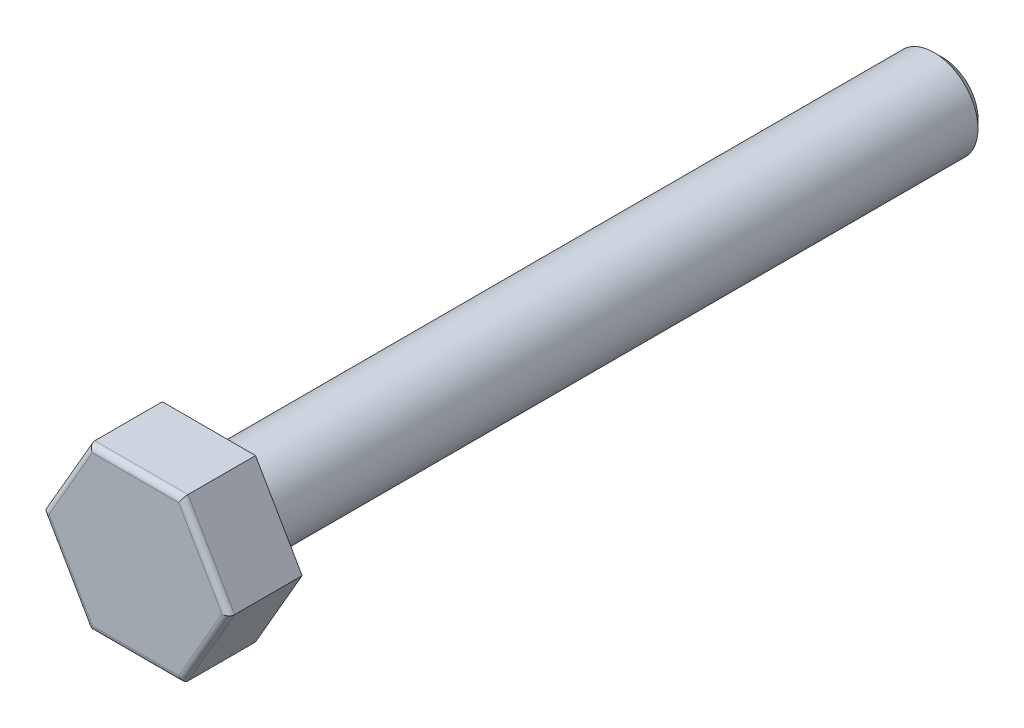
SolidWorks part; units mm, degrees
ref_plane "Front Plane" through (0, 0, 0) normal (0, 0, 1) x (1, 0, 0)
ref_plane "Top Plane" through (0, 0, 0) normal (0, 1, 0) x (1, 0, 0)
ref_plane "Right Plane" through (0, 0, 0) normal (1, 0, 0) x (0, 0, -1)
sketch "Sketch1" plane through (0, 0, 0) normal (0, 0, 1) x (1, 0, 0)
  line L1 (3.1754, 0) -> (1.5877, 2.75)
  line L2 (1.5877, 2.75) -> (-1.5877, 2.75)
  line L3 (-1.5877, 2.75) -> (-3.1754, 0)
  line L4 (-3.1754, 0) -> (-1.5877, -2.75)
  line L5 (-1.5877, -2.75) -> (1.5877, -2.75)
  line L6 (1.5877, -2.75) -> (3.1754, 0)
  circle A0 centre (0, 0) radius 2.85 construction
  circle A1 centre (0, 0) radius 2.75 construction
  dimension "D1" = 5.7
  dimension "D2" = 5.5
extrude "Boss-Extrude1" add sketch "Sketch1" along normal blind 2.5
sketch "Sketch2" plane through (0, 0, 0) normal (0, 0, -1) x (-1, 0, 0)
  circle A0 centre (0, 0) radius 1.5
  dimension "D1" = 3
extrude "Boss-Extrude2" add sketch "Sketch2" along normal blind 25
chamfer "Chamfer1" distance 0.3 angle 45 1 edges at (-1.5, 0, -25)
fillet "Fillet1" radius 0.2 6 edges at (0, -2.75, 2.5) (-2.3816, -1.375, 2.5) (-2.3816, 1.375, 2.5) (0, 2.75, 2.5) (2.3816, 1.375, 2.5) (2.3816, -1.375, 2.5)
